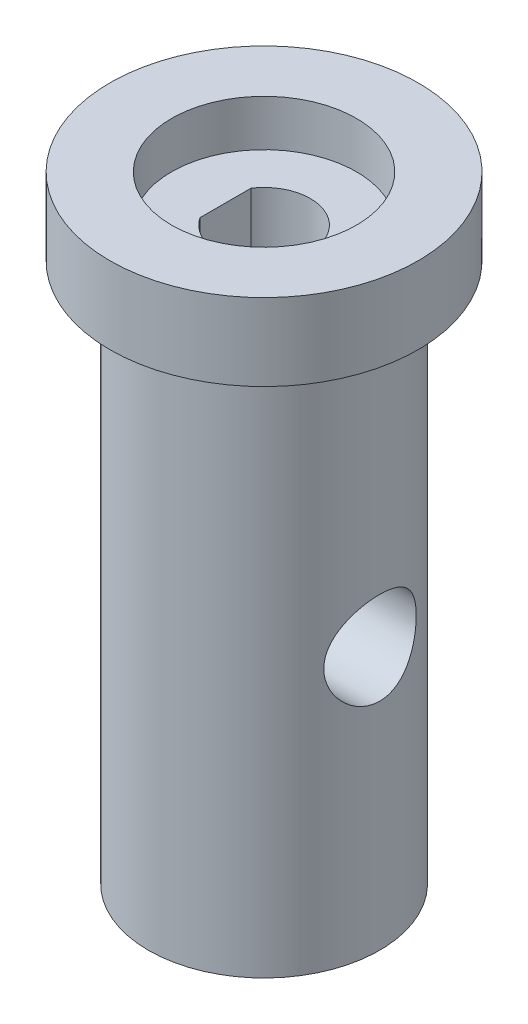
SolidWorks part; units mm, degrees
material "3003 Alloy"
ref_plane "Front Plane" through (0, 0, 0) normal (0, 0, 1) x (1, 0, 0)
ref_plane "Top Plane" through (0, 0, 0) normal (0, 1, 0) x (1, 0, 0)
ref_plane "Right Plane" through (0, 0, 0) normal (1, 0, 0) x (0, 0, -1)
sketch "Sketch1" plane through (0, 0, 0) normal (0, 1, 0) x (1, 0, 0)
  circle A0 centre (0, 0) radius 10
  dimension "D1" = 20
extrude "MetalStock" add sketch "Sketch1" against normal blind 40 contours A0
sketch "Sketch2" plane through (0, 0, 0) normal (0, 1, 0) x (1, 0, 0)
  circle A1 centre (0, 0) radius 7.5
  dimension "D1" = 15
extrude "ExteriorLathe" cut sketch "Sketch2" against normal up to surface (35 mm away) from offset 5 flip side to cut up to face at (0, -40, 10) offset against normal yes
sketch "Sketch6" plane through (0, 0, 0) normal (0, 1, 0) x (1, 0, 0)
  circle A1 centre (0, 0) radius 3
  dimension "D1" = 6
extrude "ShaftHole for Gearbox" cut sketch "Sketch6" against normal through all
sketch "Sketch7" plane through (0, 0, 0) normal (0, 1, 0) x (1, 0, 0)
  line L1 (-4.5, 3) -> (-2.5, 3)
  line L2 (-4.5, 3) -> (-4.5, -3)
  line L3 (-4.5, -3) -> (-2.5, -3)
  line L4 (-2.5, 3) -> (-2.5, -3)
  line L5 (-4.5, 3) -> (-2.5, -3) construction
  line L6 (-4.5, -3) -> (-2.5, 3) construction
  circle A1 centre (0, 0) radius 3 construction
  point P0 (-3.5, 0)
  dimension "D1" = 2.5
  dimension "D2" = 2
extrude "Key for Gearbox" add sketch "Sketch7" against normal blind 12 from surface at 0 starting at face at (0, 0, 3)
sketch "Sketch8" plane through (0, 0, 0) normal (1, 0, 0) x (0, 0, -1)
  line L0 (-7.5, -40) -> (7.5, -40) construction
  circle A3 centre (0, -23) radius 3
  dimension "D1" = 6
  dimension "D3" = 17
extrude "SideScrewHole" cut sketch "Sketch8" against normal through all both and the other way through all
sketch "Sketch9" plane through (0, 0, 0) normal (0, 1, 0) x (1, 0, 0)
  circle A0 centre (0, 0) radius 6
  dimension "D1" = 12
extrude "GearboxCounterSink" cut sketch "Sketch9" against normal blind 3
